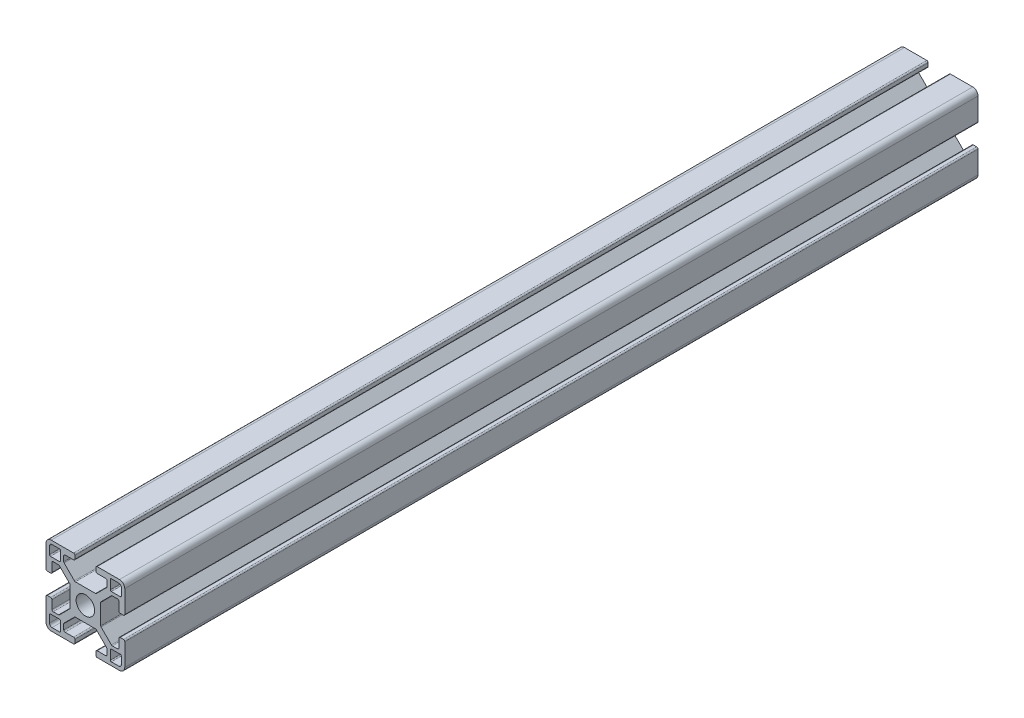
SolidWorks part; units mm, degrees
ref_plane "Front Plane" through (0, 0, 0) normal (0, 0, 1) x (1, 0, 0)
ref_plane "Top Plane" through (0, 0, 0) normal (0, 1, 0) x (1, 0, 0)
ref_plane "Right Plane" through (0, 0, 0) normal (1, 0, 0) x (0, 0, -1)
sketch "Sketch1" plane through (0, 0, 0) normal (0, 0, 1) x (1, 0, 0)
  line L0 (3.9799, -2.4733) -> (3.1981, -1.4942) construction
  line L1 (1.4942, -3.1981) -> (2.4733, -3.9799) construction
  line L2 (-2.4733, -3.9799) -> (-1.4942, -3.1981) construction
  line L3 (-3.1981, -1.4942) -> (-3.9799, -2.4733) construction
  line L4 (-3.9799, 2.4733) -> (-3.1981, 1.4942) construction
  line L5 (-1.4942, 3.1981) -> (-2.4733, 3.9799) construction
  line L6 (2.4733, 3.9799) -> (1.4942, 3.1981) construction
  line L7 (3.1981, 1.4942) -> (3.9799, 2.4733) construction
  line L8 (-12.6999, -13.6999) -> (-9.881, -13.6999)
  line L9 (-13.6999, -9.881) -> (-13.6999, -12.6999)
  line L10 (-9.88, -9.5) -> (-13.3189, -9.5)
  line L11 (-9.5, -13.3189) -> (-9.5, -9.88)
  line L12 (13.6999, -12.6999) -> (13.6999, -9.881)
  line L13 (9.881, -13.6999) -> (12.6999, -13.6999)
  line L14 (9.5, -9.88) -> (9.5, -13.3189)
  line L15 (13.3189, -9.5) -> (9.88, -9.5)
  line L16 (9.88, 9.5) -> (13.3189, 9.5)
  line L17 (9.5, 13.3189) -> (9.5, 9.88)
  line L18 (12.6999, 13.6999) -> (9.881, 13.6999)
  line L19 (13.6999, 9.881) -> (13.6999, 12.6999)
  line L20 (-13.6999, 12.6999) -> (-13.6999, 9.881)
  line L21 (-9.881, 13.6999) -> (-12.6999, 13.6999)
  line L22 (-9.5, 9.88) -> (-9.5, 13.3189)
  line L23 (-13.3189, 9.5) -> (-9.88, 9.5)
  line L24 (14.4999, -4) -> (13.2425, -4)
  line L25 (12.7425, -4.5) -> (12.7425, -7.7325)
  line L26 (12.2428, -8.25) -> (10.2602, -8.25)
  line L27 (9.9066, -8.1035) -> (5.9811, -4.178)
  line L28 (5.8347, -3.8245) -> (5.8347, -1.0125)
  line L29 (5.8347, -1.0125) -> (5.3247, -0.0625) construction
  line L30 (5.3247, -0.0625) -> (5.8347, 0.8875) construction
  line L31 (5.8347, 0.8875) -> (5.8347, 3.8245)
  line L32 (5.9811, 4.178) -> (9.9066, 8.1035)
  line L33 (10.2602, 8.25) -> (12.2428, 8.25)
  line L34 (12.7425, 7.7325) -> (12.7425, 4.5)
  line L35 (13.2425, 4) -> (14.4999, 4)
  line L36 (14.9999, 4.5) -> (14.9999, 12.9999)
  line L37 (12.9999, 14.9999) -> (4.5, 14.9999)
  line L38 (4, 14.4999) -> (4, 13.2425)
  line L39 (4.5, 12.7425) -> (7.7325, 12.7425)
  line L40 (8.25, 12.2428) -> (8.25, 10.2602)
  line L41 (8.1035, 9.9066) -> (4.178, 5.9811)
  line L42 (3.8245, 5.8347) -> (0.95, 5.8347)
  line L43 (0.95, 5.8347) -> (0, 5.3247) construction
  line L44 (0, 5.3247) -> (-0.95, 5.8347) construction
  line L45 (-0.95, 5.8347) -> (-3.8245, 5.8347)
  line L46 (-4.178, 5.9811) -> (-8.1035, 9.9066)
  line L47 (-8.25, 10.2602) -> (-8.25, 12.2428)
  line L48 (-7.7325, 12.7425) -> (-4.5, 12.7425)
  line L49 (-4, 13.2425) -> (-4, 14.4999)
  line L50 (-4.5, 14.9999) -> (-12.9999, 14.9999)
  line L51 (-14.9999, 12.9999) -> (-14.9999, 4.5)
  line L52 (-14.4999, 4) -> (-13.2425, 4)
  line L53 (-12.7425, 4.5) -> (-12.7425, 7.7325)
  line L54 (-12.2428, 8.25) -> (-10.2602, 8.25)
  line L55 (-9.9066, 8.1035) -> (-5.9811, 4.178)
  line L56 (-5.8347, 3.8245) -> (-5.8347, 0.8875)
  line L57 (-5.8347, 0.8875) -> (-5.3247, -0.0625) construction
  line L58 (-5.3247, -0.0625) -> (-5.8347, -1.0125) construction
  line L59 (-5.8347, -1.0125) -> (-5.8347, -3.8245)
  line L60 (-5.9811, -4.178) -> (-9.9066, -8.1035)
  line L61 (-10.2602, -8.25) -> (-12.2428, -8.25)
  line L62 (-12.7425, -7.7325) -> (-12.7425, -4.5)
  line L63 (-13.2425, -4) -> (-14.4999, -4)
  line L64 (-14.9999, -4.5) -> (-14.9999, -12.9999)
  line L65 (-12.9999, -14.9999) -> (-4.5, -14.9999)
  line L66 (-4, -14.4999) -> (-4, -13.2425)
  line L67 (-4.5, -12.7425) -> (-7.7325, -12.7425)
  line L68 (-8.25, -12.2428) -> (-8.25, -10.2602)
  line L69 (-8.1035, -9.9066) -> (-4.178, -5.9811)
  line L70 (-3.8245, -5.8347) -> (-0.95, -5.8347)
  line L71 (-0.95, -5.8347) -> (0, -5.3247) construction
  line L72 (0, -5.3247) -> (0.95, -5.8347) construction
  line L73 (0.95, -5.8347) -> (3.8245, -5.8347)
  line L74 (4.178, -5.9811) -> (8.1035, -9.9066)
  line L75 (8.25, -10.2602) -> (8.25, -12.2428)
  line L76 (7.7325, -12.7425) -> (4.5, -12.7425)
  line L77 (4, -13.2425) -> (4, -14.4999)
  line L78 (4.5, -14.9999) -> (12.9999, -14.9999)
  line L79 (14.9999, -12.9999) -> (14.9999, -4.5)
  line L80 (-5.8347, -1.0125) -> (-5.8347, 0.8875)
  line L81 (-0.95, 5.8347) -> (0.95, 5.8347)
  line L82 (5.8347, 0.8875) -> (5.8347, -1.0125)
  line L83 (-0.95, -5.8347) -> (0.95, -5.8347)
  arc A0 (2.4733, -3.9799) -> (3.9799, -2.4733) centre (3.1422, -3.1422) ccw construction
  arc A1 (-1.4942, -3.1981) -> (1.4942, -3.1981) centre (0, 0) ccw construction
  arc A2 (-3.9799, -2.4733) -> (-2.4733, -3.9799) centre (-3.1422, -3.1422) ccw construction
  arc A3 (-3.1981, 1.4942) -> (-3.1981, -1.4942) centre (0, 0) ccw construction
  arc A4 (-2.4733, 3.9799) -> (-3.9799, 2.4733) centre (-3.1422, 3.1422) ccw construction
  arc A5 (1.4942, 3.1981) -> (-1.4942, 3.1981) centre (0, 0) ccw construction
  arc A6 (3.9799, 2.4733) -> (2.4733, 3.9799) centre (3.1422, 3.1422) ccw construction
  arc A7 (3.1981, -1.4942) -> (3.1981, 1.4942) centre (0, 0) ccw construction
  arc A8 (-13.6999, -12.6999) -> (-12.6999, -13.6999) centre (-12.6999, -12.6999) ccw
  arc A9 (-13.3189, -9.5) -> (-13.6999, -9.881) centre (-13.3189, -9.881) ccw
  arc A10 (-9.5, -9.88) -> (-9.88, -9.5) centre (-9.88, -9.88) ccw
  arc A11 (-9.881, -13.6999) -> (-9.5, -13.3189) centre (-9.881, -13.3189) ccw
  arc A12 (12.6999, -13.6999) -> (13.6999, -12.6999) centre (12.6999, -12.6999) ccw
  arc A13 (9.5, -13.3189) -> (9.881, -13.6999) centre (9.881, -13.3189) ccw
  arc A14 (9.88, -9.5) -> (9.5, -9.88) centre (9.88, -9.88) ccw
  arc A15 (13.6999, -9.881) -> (13.3189, -9.5) centre (13.3189, -9.881) ccw
  arc A16 (9.5, 9.88) -> (9.88, 9.5) centre (9.88, 9.88) ccw
  arc A17 (9.881, 13.6999) -> (9.5, 13.3189) centre (9.881, 13.3189) ccw
  arc A18 (13.6999, 12.6999) -> (12.6999, 13.6999) centre (12.6999, 12.6999) ccw
  arc A19 (13.3189, 9.5) -> (13.6999, 9.881) centre (13.3189, 9.881) ccw
  arc A20 (14.9999, -4.5) -> (14.4999, -4) centre (14.4999, -4.5) ccw
  arc A21 (13.2425, -4) -> (12.7425, -4.5) centre (13.2425, -4.5) ccw
  arc A22 (12.2428, -8.25) -> (12.7425, -7.7325) centre (12.2428, -7.75) ccw
  arc A23 (9.9066, -8.1035) -> (10.2602, -8.25) centre (10.2602, -7.75) ccw
  arc A24 (5.8347, -3.8245) -> (5.9811, -4.178) centre (6.3347, -3.8245) ccw
  arc A25 (5.9811, 4.178) -> (5.8347, 3.8245) centre (6.3347, 3.8245) ccw
  arc A26 (10.2602, 8.25) -> (9.9066, 8.1035) centre (10.2602, 7.75) ccw
  arc A27 (12.7425, 7.7325) -> (12.2428, 8.25) centre (12.2428, 7.75) ccw
  arc A28 (12.7425, 4.5) -> (13.2425, 4) centre (13.2425, 4.5) ccw
  arc A29 (14.4999, 4) -> (14.9999, 4.5) centre (14.4999, 4.5) ccw
  arc A30 (14.9999, 12.9999) -> (12.9999, 14.9999) centre (12.9999, 12.9999) ccw
  arc A31 (4.5, 14.9999) -> (4, 14.4999) centre (4.5, 14.4999) ccw
  arc A32 (4, 13.2425) -> (4.5, 12.7425) centre (4.5, 13.2425) ccw
  arc A33 (8.25, 12.2428) -> (7.7325, 12.7425) centre (7.75, 12.2428) ccw
  arc A34 (8.1035, 9.9066) -> (8.25, 10.2602) centre (7.75, 10.2602) ccw
  arc A35 (3.8245, 5.8347) -> (4.178, 5.9811) centre (3.8245, 6.3347) ccw
  arc A36 (-4.178, 5.9811) -> (-3.8245, 5.8347) centre (-3.8245, 6.3347) ccw
  arc A37 (-8.25, 10.2602) -> (-8.1035, 9.9066) centre (-7.75, 10.2602) ccw
  arc A38 (-7.7325, 12.7425) -> (-8.25, 12.2428) centre (-7.75, 12.2428) ccw
  arc A39 (-4.5, 12.7425) -> (-4, 13.2425) centre (-4.5, 13.2425) ccw
  arc A40 (-4, 14.4999) -> (-4.5, 14.9999) centre (-4.5, 14.4999) ccw
  arc A41 (-12.9999, 14.9999) -> (-14.9999, 12.9999) centre (-12.9999, 12.9999) ccw
  arc A42 (-14.9999, 4.5) -> (-14.4999, 4) centre (-14.4999, 4.5) ccw
  arc A43 (-13.2425, 4) -> (-12.7425, 4.5) centre (-13.2425, 4.5) ccw
  arc A44 (-12.2428, 8.25) -> (-12.7425, 7.7325) centre (-12.2428, 7.75) ccw
  arc A45 (-9.9066, 8.1035) -> (-10.2602, 8.25) centre (-10.2602, 7.75) ccw
  arc A46 (-5.8347, 3.8245) -> (-5.9811, 4.178) centre (-6.3347, 3.8245) ccw
  arc A47 (-5.9811, -4.178) -> (-5.8347, -3.8245) centre (-6.3347, -3.8245) ccw
  arc A48 (-10.2602, -8.25) -> (-9.9066, -8.1035) centre (-10.2602, -7.75) ccw
  arc A49 (-12.7425, -7.7325) -> (-12.2428, -8.25) centre (-12.2428, -7.75) ccw
  arc A50 (-12.7425, -4.5) -> (-13.2425, -4) centre (-13.2425, -4.5) ccw
  arc A51 (-14.4999, -4) -> (-14.9999, -4.5) centre (-14.4999, -4.5) ccw
  arc A52 (-14.9999, -12.9999) -> (-12.9999, -14.9999) centre (-12.9999, -12.9999) ccw
  arc A53 (-4.5, -14.9999) -> (-4, -14.4999) centre (-4.5, -14.4999) ccw
  arc A54 (-4, -13.2425) -> (-4.5, -12.7425) centre (-4.5, -13.2425) ccw
  arc A55 (-8.25, -12.2428) -> (-7.7325, -12.7425) centre (-7.75, -12.2428) ccw
  arc A56 (-8.1035, -9.9066) -> (-8.25, -10.2602) centre (-7.75, -10.2602) ccw
  arc A57 (-3.8245, -5.8347) -> (-4.178, -5.9811) centre (-3.8245, -6.3347) ccw
  arc A58 (4.178, -5.9811) -> (3.8245, -5.8347) centre (3.8245, -6.3347) ccw
  arc A59 (8.25, -10.2602) -> (8.1035, -9.9066) centre (7.75, -10.2602) ccw
  arc A60 (7.7325, -12.7425) -> (8.25, -12.2428) centre (7.75, -12.2428) ccw
  arc A61 (4.5, -12.7425) -> (4, -13.2425) centre (4.5, -13.2425) ccw
  arc A62 (4, -14.4999) -> (4.5, -14.9999) centre (4.5, -14.4999) ccw
  arc A63 (12.9999, -14.9999) -> (14.9999, -12.9999) centre (12.9999, -12.9999) ccw
  arc A64 (-12.6999, 13.6999) -> (-13.6999, 12.6999) centre (-12.6999, 12.6999) ccw
  arc A65 (-9.5, 13.3189) -> (-9.881, 13.6999) centre (-9.881, 13.3189) ccw
  arc A66 (-9.88, 9.5) -> (-9.5, 9.88) centre (-9.88, 9.88) ccw
  arc A67 (-13.6999, 9.881) -> (-13.3189, 9.5) centre (-13.3189, 9.881) ccw
  circle A68 centre (0, 0) radius 3.53
extrude "Boss-Extrude1" add sketch "Sketch1" along normal mid plane 325
